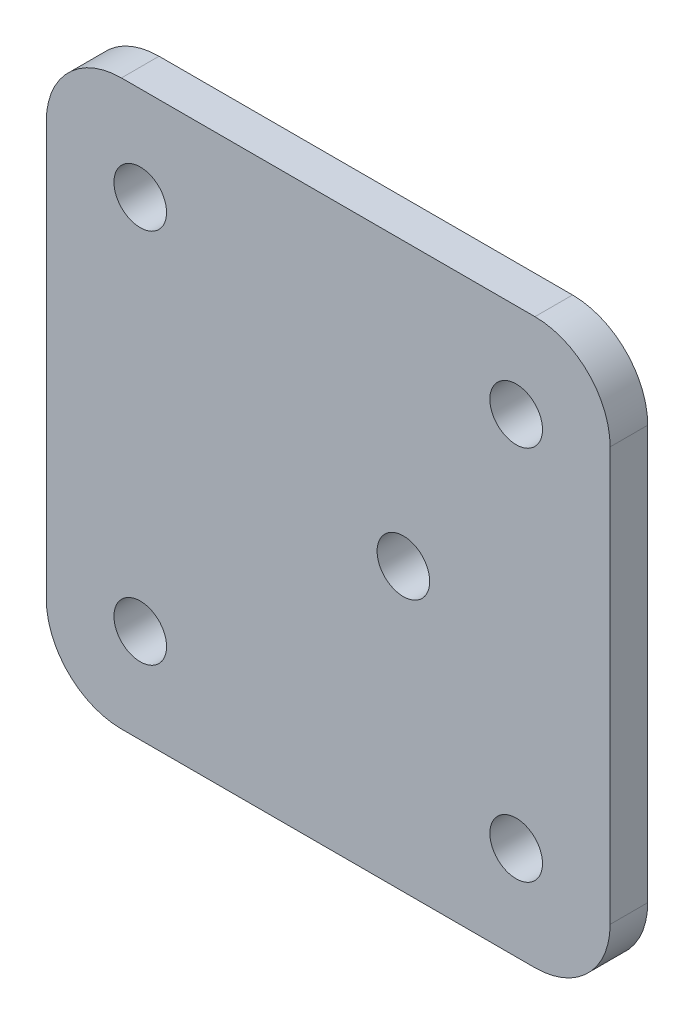
SolidWorks part; units mm, degrees
material "1.0545 (S355N)"
ref_plane "Front Plane" through (0, 0, 0) normal (0, 0, 1) x (1, 0, 0)
ref_plane "Top Plane" through (0, 0, 0) normal (0, 1, 0) x (1, 0, 0)
ref_plane "Right Plane" through (0, 0, 0) normal (1, 0, 0) x (0, 0, -1)
sketch "Sketch1" plane through (0, 0, 0) normal (0, 0, 1) x (1, 0, 0)
  line L0 (-36.5658, 0) -> (63.1228, 0) construction
  line L1 (0, 43.3719) -> (0, -42.4377) construction
  line L2 (-37.5, 37.5) -> (37.5, 37.5)
  line L3 (-37.5, 37.5) -> (-37.5, -37.5)
  line L4 (-37.5, -37.5) -> (37.5, -37.5)
  line L5 (37.5, 37.5) -> (37.5, -37.5)
  dimension "D1" = 75
extrude "Boss-Extrude1" add sketch "Sketch1" along normal blind 5
sketch "Sketch2" plane through (0, 0, 5) normal (0, 0, 1) x (1, 0, 0)
  line L0 (0, 39.5963) -> (0, -41.4866) construction
  line L1 (-42.2825, 0) -> (50.8385, 0) construction
  point P5 (-25, 25)
  point P6 (25, 25)
  point P7 (25, -25)
  point P8 (-25, -25)
  dimension "D1" = 50
  dimension "D2" = 50
hole_wizard "M6 Clearance Hole1" positions "Sketch3" profile "Sketch4" hole size "M6" standard "ISO" end condition through all
sketch "Sketch3" plane through (0, 0, 5) normal (0, 0, 1) x (1, 0, 0)
  point P0 (-25, 25)
  point P3 (-25, -25)
  point P6 (25, -25)
  point P9 (25, 25)
sketch "Sketch4" plane through (-25, 25, 5) normal (1, 0, 0) x (0, -1, 0)
  line L0 (0, 0) -> (0, 5)
  line L1 (0, 5) -> (3.5, 5)
  line L2 (3.5, 5) -> (3.5, 0)
  line L5 (3.5, 0) -> (0, 0)
  line L11 (0, -6.35) -> (0, 107.95) construction
  dimension "Thru Hole Dia." = 7
  dimension "Thru Hole Depth" = 5
fillet "Fillet1" radius 10 4 edges at (-37.5, 37.5, 2.5) (-37.5, -37.5, 2.5) (37.5, -37.5, 2.5) (37.5, 37.5, 2.5)
sketch "Sketch5" plane through (0, 0, 5) normal (0, 0, 1) x (1, 0, 0)
  circle A0 centre (25, 25) radius 3.5 construction
  point P0 (10, 0)
  dimension "D1" = 15
hole_wizard "M6 Clearance Hole2" positions "Sketch8" profile "Sketch7" hole size "M6" standard "ISO" end condition through all
sketch "Sketch8" plane through (0, 0, 5) normal (0, 0, 1) x (1, 0, 0)
  point P0 (10, 0)
sketch "Sketch7" plane through (10, 0, 5) normal (1, 0, 0) x (0, -1, 0)
  line L0 (0, 0) -> (0, 5)
  line L1 (0, 5) -> (3.5, 5)
  line L2 (3.5, 5) -> (3.5, 0)
  line L5 (3.5, 0) -> (0, 0)
  line L11 (0, -6.35) -> (0, 107.95) construction
  dimension "Thru Hole Dia." = 7
  dimension "Thru Hole Depth" = 5
